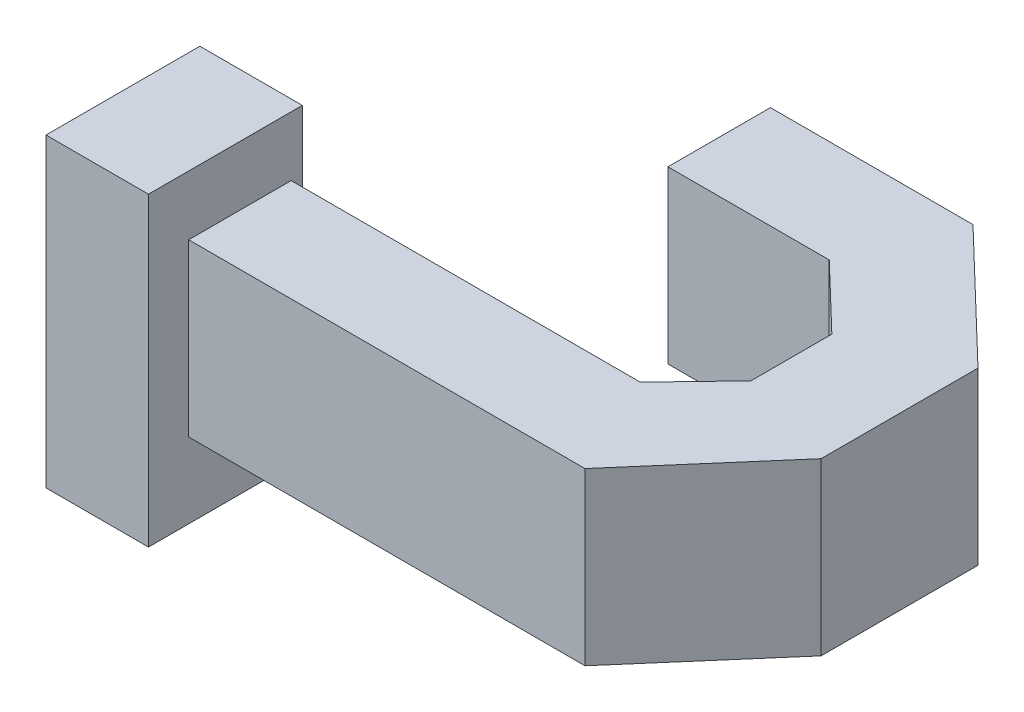
SolidWorks part; units mm, degrees
ref_plane "Спереди" through (0, 0, 0) normal (0, 0, 1) x (1, 0, 0)
ref_plane "Сверху" through (0, 0, 0) normal (0, 1, 0) x (1, 0, 0)
ref_plane "Справа" through (0, 0, 0) normal (1, 0, 0) x (0, 0, -1)
other "Configuration Table"
sketch "Эскиз1" plane through (0, 0, 0) normal (0, 1, 0) x (1, 0, 0)
  line L0 (0, 0) -> (11.6005, 0)
  line L1 (11.6005, 0) -> (14.8054, 3.7074)
  line L2 (14.8054, 3.7074) -> (14.8054, 8.2997)
  line L3 (14.8054, 8.2997) -> (11.0936, 11.8643)
  line L4 (11.0936, 11.8643) -> (5.1646, 11.8643)
  line L5 (5.1646, 11.8643) -> (5.1646, 8.8643)
  line L6 (5.1646, 8.8643) -> (9.8864, 8.8643)
  line L7 (9.8864, 8.8643) -> (11.8054, 7.0213)
  line L8 (11.8054, 7.0213) -> (11.8054, 4.6523)
  line L9 (11.8054, 4.6523) -> (10.2186, 3)
  line L10 (10.2186, 3) -> (0, 3)
  line L11 (0, 3) -> (0, 0)
  point P3 (11.6582, 0)
  point P14 (10.8338, 3.0978)
  point P15 (11.8054, 4.6523)
  dimension "D1" = 3
  dimension "D2" = 3
  dimension "D3" = 3
  dimension "D4" = 3
  dimension "D5" = 3
extrude "Бобышка-Вытянуть1" add sketch "Эскиз1" along normal blind 5
sketch "Эскиз2" plane through (0, 0, 0) normal (-1, 0, 0) x (0, 0, 1)
  line L1 (-3.3263, 6.7437) -> (1.1768, 6.7437)
  line L2 (-3.3263, 6.7437) -> (-3.3263, -2.2025)
  line L3 (-3.3263, -2.2025) -> (1.1768, -2.2025)
  line L4 (1.1768, 6.7437) -> (1.1768, -2.2025)
  line L5 (-1.0747, -2.2025) -> (-1.0747, 6.7437) construction
  line L6 (-3.3263, 2.2706) -> (1.1768, 2.2706) construction
  point P348 (-1.0747, 2.2706)
extrude "Бобышка-Вытянуть2" add sketch "Эскиз2" along normal blind 3
